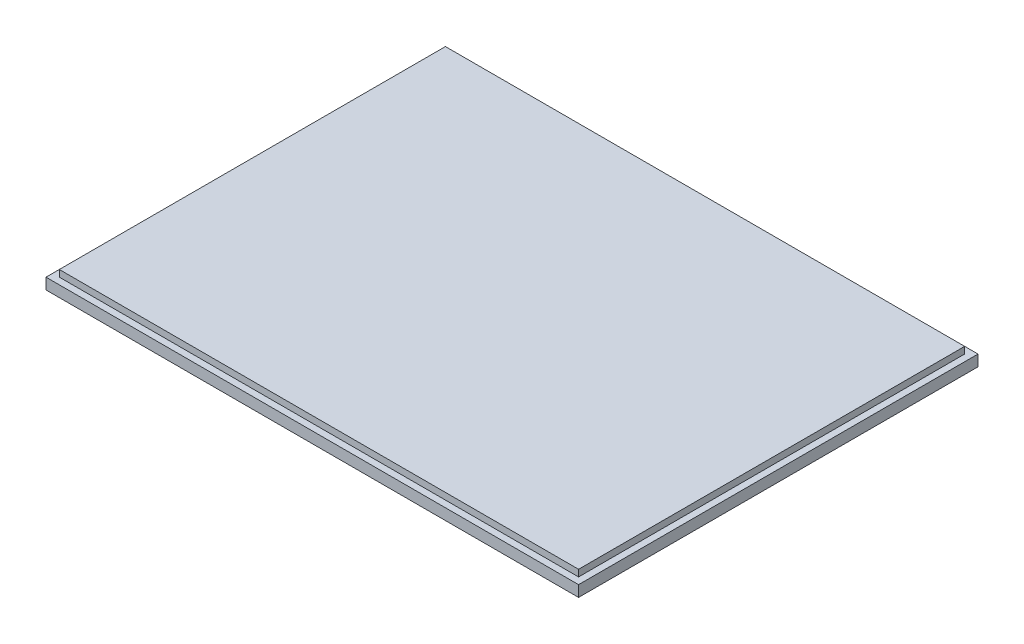
SolidWorks part; units mm, degrees
ref_plane "Front Plane" through (0, 0, 0) normal (0, 0, 1) x (1, 0, 0)
ref_plane "Top Plane" through (0, 0, 0) normal (0, 1, 0) x (1, 0, 0)
ref_plane "Right Plane" through (0, 0, 0) normal (1, 0, 0) x (0, 0, -1)
sketch "Sketch1" plane through (0, 0, 0) normal (0, 1, 0) x (1, 0, 0)
  line L1 (-60, 45) -> (60, 45)
  line L2 (-60, 45) -> (-60, -45)
  line L3 (-60, -45) -> (60, -45)
  line L4 (60, 45) -> (60, -45)
  line L5 (-60, 45) -> (60, -45) construction
  line L6 (-60, -45) -> (60, 45) construction
  point P0 (0, 0)
  dimension "D1" = 120
  dimension "D2" = 90
extrude "Boss-Extrude1" add sketch "Sketch1" along normal blind 4
sketch "Sketch2" plane through (0, 4, 0) normal (0, 1, 0) x (1, 0, 0)
  line L0 (60, -45) -> (60, 45) construction
  line L5 (-58.5, 43.5) -> (58.5, 43.5)
  line L6 (-58.5, 43.5) -> (-58.5, -43.5)
  line L7 (-58.5, -43.5) -> (58.5, -43.5)
  line L8 (58.5, 43.5) -> (58.5, -43.5)
  line L9 (-58.5, 43.5) -> (58.5, -43.5) construction
  line L10 (-58.5, -43.5) -> (58.5, 43.5) construction
  line L11 (-60, -45) -> (60, -45) construction
  point P0 (0, 0)
  dimension "D1" = 1.5
  dimension "D2" = 1.5
extrude "Cut-Extrude1" cut sketch "Sketch2" against normal blind 1.5 flip side to cut
